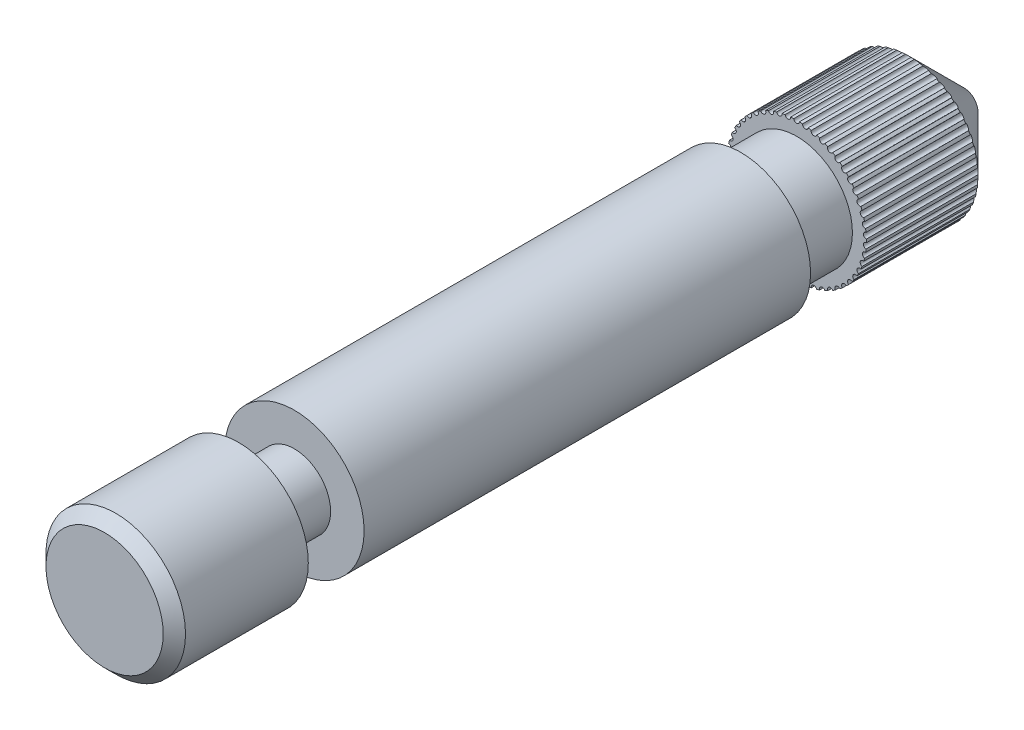
SolidWorks part; units mm, degrees
ref_plane "Front Plane" through (0, 0, 0) normal (0, 0, 1) x (1, 0, 0)
ref_plane "Top Plane" through (0, 0, 0) normal (0, 1, 0) x (1, 0, 0)
ref_plane "Right Plane" through (0, 0, 0) normal (1, 0, 0) x (0, 0, -1)
sketch "Sketch1" plane through (0, 0, 0) normal (0, 0, 1) x (1, 0, 0)
  circle A0 centre (0, 0) radius 1.25
  dimension "D1" = 2.5
extrude "Boss-Extrude1" add sketch "Sketch1" against normal blind 15.4
sketch "Sketch2" plane through (0, 0, 0) normal (1, 0, 0) x (0, 0, -1)
  line L0 (0, 0) -> (15.4, 0) construction
  line L1 (15.4, -1.25) -> (15.4, 1.25) construction
  line L2 (15.4, 1.25) -> (0, 1.25) construction
  line L3 (3.4, 1.25) -> (2.4, 1.25)
  line L6 (2.4, 1.25) -> (2.4, 0.65)
  line L7 (2.4, 0.65) -> (3.4, 0.65)
  line L8 (3.4, 1.25) -> (3.4, 0.65)
  dimension "D1" = 3.4
  dimension "D2" = 1
  dimension "D3" = 1.3
revolve "Cut-Revolve1" cut sketch "Sketch2" angle 360 about L0
sketch "Sketch3" plane through (0, 0, 0) normal (1, 0, 0) x (0, 0, -1)
  line L0 (15.4, 1.25) -> (3.4, 1.25) construction
  line L1 (12.4, 1.25) -> (11.4, 1.25)
  line L2 (12.4, 1.25) -> (12.4, 1)
  line L3 (12.4, 1) -> (11.4, 1)
  line L4 (11.4, 1.25) -> (11.4, 1)
  line L5 (0, 0) -> (15.4, 0) construction
  line L6 (0, 1.25) -> (0, -1.25) construction
  line L7 (15.4, -1.25) -> (15.4, 1.25) construction
  dimension "D1" = 2
  dimension "D2" = 3
  dimension "D3" = 1
revolve "Cut-Revolve2" cut sketch "Sketch3" angle 360 about L5
chamfer "Chamfer1" distance 1 angle 45 1 edges at (1.25, 0, -15.4)
chamfer "Chamfer2" distance 0.2 angle 45 1 edges at (1.25, 0, 0)
sketch "Sketch4" plane through (0, 0, -12.4) normal (0, 0, 1) x (1, 0, 0)
  line L0 (0, 0) -> (0, 1.25) construction
  circle A0 centre (0, 0) radius 1.25 construction
  circle A1 centre (0, 1.25) radius 0.05
  dimension "D1" = 0.1
extrude "Cut-Extrude2" cut sketch "Sketch4" against normal up to next contours A1
pattern_circular "CirPattern2" count 50 over 360 about axis through (0, 0, 0) along (0, 0, 1) of "Cut-Extrude2"
